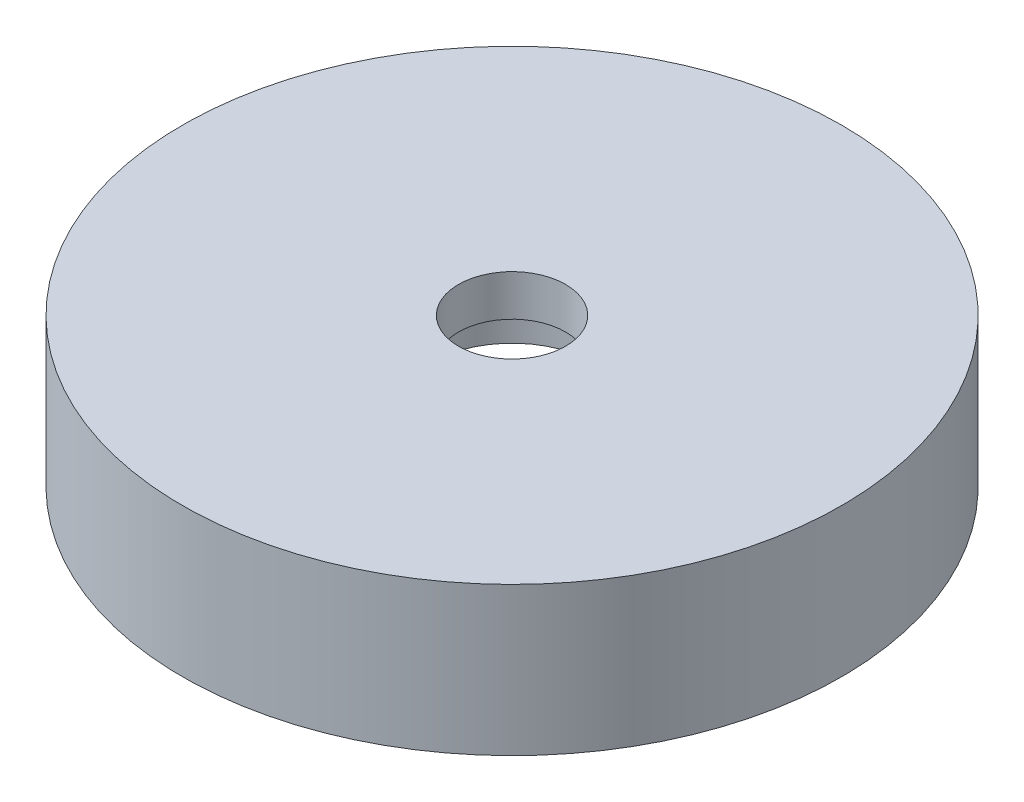
SolidWorks part; units mm, degrees
ref_plane "Plano frontal" through (0, 0, 0) normal (0, 0, 1) x (1, 0, 0)
ref_plane "Plano superior" through (0, 0, 0) normal (0, 1, 0) x (1, 0, 0)
ref_plane "Plano direito" through (0, 0, 0) normal (1, 0, 0) x (0, 0, -1)
sketch "Esboço1" plane through (0, 0, 0) normal (0, 0, 1) x (1, 0, 0)
  line L0 (0, 0) -> (0, 22.7862) construction
  line L1 (0, 0) -> (19.7974, 0) construction
  line L2 (3.25, 14) -> (3.25, 11.5)
  line L3 (3.25, 11.5) -> (5, 11.5)
  line L4 (5, 11.5) -> (5, 9)
  line L5 (5, 9) -> (17.5, 9)
  line L6 (17.5, 9) -> (17.5, 5)
  line L7 (17.5, 5) -> (20, 5)
  line L8 (20, 5) -> (20, 14)
  line L9 (20, 14) -> (3.25, 14)
  dimension "D1" = 40
  dimension "D2" = 35
  dimension "D3" = 5
  dimension "D4" = 2.5
  dimension "D5" = 10
  dimension "D6" = 6.5
  dimension "D7" = 9
  dimension "D8" = 9
revolve "Revolução1" add sketch "Esboço1" angle 360 about L0
